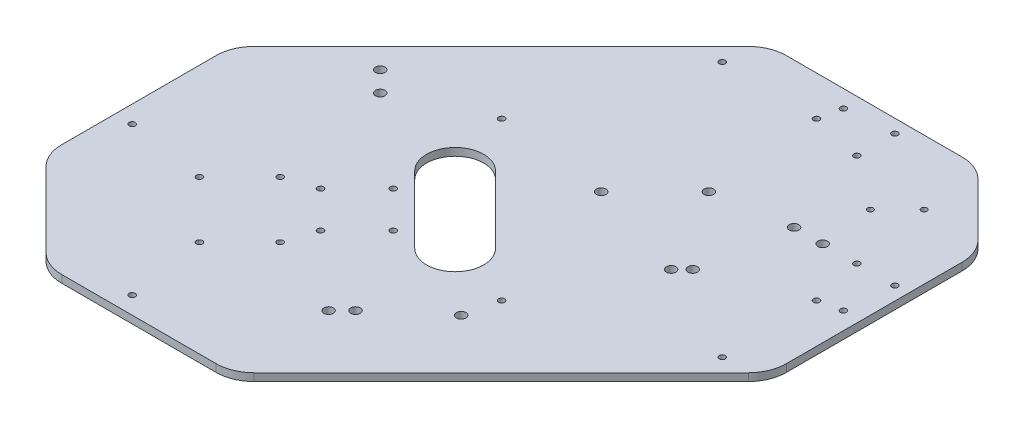
SolidWorks part; units mm, degrees
ref_plane "Front Plane" through (0, 0, 0) normal (0, 0, 1) x (1, 0, 0)
ref_plane "Top Plane" through (0, 0, 0) normal (0, 1, 0) x (1, 0, 0)
ref_plane "Right Plane" through (0, 0, 0) normal (1, 0, 0) x (0, 0, -1)
sketch "Sketch2" plane through (0, 0, 0) normal (0, 1, 0) x (1, 0, 0)
  line L0 (-139.1421, 9.3503) -> (-9.3503, 139.1421)
  line L1 (-150, 150) -> (150, 150) construction
  line L2 (-150, 150) -> (-150, -150) construction
  line L3 (-150, -150) -> (150, -150) construction
  line L4 (150, 150) -> (150, -150) construction
  line L5 (111.3604, 139.1421) -> (139.1421, 111.3604)
  line L6 (-139.1421, -100.0467) -> (-100.0467, -139.1421)
  line L7 (139.1421, -9.3503) -> (9.3503, -139.1421)
  line L8 (150, 150) -> (-150, -150) construction
  line L9 (-29.7918, 5.5635) -> (5.5635, -29.7918) construction
  line L10 (-19.1852, 16.1701) -> (16.1701, -19.1852)
  line L11 (-145, -4.7918) -> (-145, -85.9045)
  line L12 (-85.9045, -145) -> (-4.7918, -145)
  line L13 (145, 4.7918) -> (145, 97.2183)
  line L14 (4.7918, 145) -> (97.2183, 145)
  line L15 (-135.8579, -58.0761) -> (-58.0761, -135.8579) construction
  line L16 (41.4591, 124.1906) -> (124.1906, 41.4591) construction
  line L17 (41.4591, 124.1906) -> (-41.2724, 41.4591) construction
  line L18 (-41.2724, 41.4591) -> (41.4591, -41.2724) construction
  line L19 (124.1906, 41.4591) -> (41.4591, -41.2724) construction
  line L20 (-40.3984, -5.0431) -> (-5.0431, -40.3984)
  line L21 (-72.9254, -43.2269) -> (-43.2269, -72.9254) construction
  line L22 (-72.9254, -43.2269) -> (-94.1386, -64.4401) construction
  line L23 (-94.1386, -64.4401) -> (-64.4401, -94.1386) construction
  line L24 (-37.9236, -18.8317) -> (-18.8317, -37.9236) construction
  line L25 (-37.9236, -18.8317) -> (-57.0155, -37.9236) construction
  line L26 (-57.0155, -37.9236) -> (-37.9236, -57.0155) construction
  line L27 (-18.8317, -37.9236) -> (-37.9236, -57.0155) construction
  line L28 (-43.2269, -72.9254) -> (-64.4401, -94.1386) construction
  line L29 (138, 68.8629) -> (118, 68.8629) construction
  line L30 (68.8629, 138) -> (68.8629, 118) construction
  line L31 (68.8629, 118) -> (118, 68.8629) construction
  line L32 (77.5216, 23.0743) -> (71.8647, 17.4175) construction
  line L33 (46.4089, 62.6723) -> (18.1246, 34.388) construction
  line L34 (-9.099, 125.2513) -> (125.2513, -9.099) construction
  line L35 (77.5216, 23.0743) -> (42.1662, 58.4297) construction
  line L36 (43.934, 135.8579) -> (135.8579, 43.934) construction
  line L37 (-95.4358, 31.8434) -> (-84.8292, 21.2368) construction
  line L38 (85, 68.8629) -> (100, 68.8629) construction
  line L39 (7.6848, -84.2391) -> (0.6137, -91.3101) construction
  arc A0 (-19.1852, 16.1701) -> (-40.3984, -5.0431) centre (-29.7918, 5.5635) ccw
  arc A1 (-5.0431, -40.3984) -> (16.1701, -19.1852) centre (5.5635, -29.7918) ccw
  circle A2 centre (-94.1386, -64.4401) radius 1.6
  circle A3 centre (-64.4401, -94.1386) radius 1.6
  arc A4 (-145, -4.7918) -> (-139.1421, 9.3503) centre (-125, -4.7918) cw
  arc A5 (-145, -85.9045) -> (-139.1421, -100.0467) centre (-125, -85.9045) ccw
  arc A6 (-85.9045, -145) -> (-100.0467, -139.1421) centre (-85.9045, -125) cw
  arc A7 (-4.7918, -145) -> (9.3503, -139.1421) centre (-4.7918, -125) ccw
  arc A8 (145, 4.7918) -> (139.1421, -9.3503) centre (125, 4.7918) cw
  arc A9 (145, 97.2183) -> (139.1421, 111.3604) centre (125, 97.2183) ccw
  arc A10 (97.2183, 145) -> (111.3604, 139.1421) centre (97.2183, 125) cw
  arc A11 (4.7918, 145) -> (-9.3503, 139.1421) centre (4.7918, 125) ccw
  circle A12 centre (-41.2724, 41.4591) radius 1.6
  circle A13 centre (41.4591, -41.2724) radius 1.6
  circle A14 centre (124.1906, 41.4591) radius 1.6
  circle A15 centre (41.4591, 124.1906) radius 1.6
  circle A16 centre (-135.8579, -58.0761) radius 1.6
  circle A17 centre (-58.0761, -135.8579) radius 1.6
  circle A18 centre (-43.2269, -72.9254) radius 1.6
  circle A19 centre (-72.9254, -43.2269) radius 1.6
  circle A20 centre (111.1091, 111.1091) radius 1.5
  circle A21 centre (96.967, 96.967) radius 1.5
  circle A22 centre (-57.0155, -37.9236) radius 1.6
  circle A23 centre (-37.9236, -57.0155) radius 1.6
  circle A24 centre (-18.8317, -37.9236) radius 1.6
  circle A25 centre (-37.9236, -18.8317) radius 1.6
  circle A26 centre (138, 68.8629) radius 1.6
  circle A27 centre (118, 68.8629) radius 1.6
  circle A28 centre (68.8629, 138) radius 1.6
  circle A29 centre (68.8629, 118) radius 1.6
  circle A30 centre (-9.099, 125.2513) radius 1.6
  circle A31 centre (125.2513, -9.099) radius 1.6
  circle A32 centre (77.5216, 23.0743) radius 2.5
  circle A33 centre (71.8647, 17.4175) radius 2.5
  circle A34 centre (43.934, 135.8579) radius 1.6
  circle A35 centre (135.8579, 43.934) radius 1.6
  circle A36 centre (18.1246, 34.388) radius 2.5
  circle A37 centre (46.4089, 62.6723) radius 2.5
  circle A38 centre (-95.4358, 31.8434) radius 2.5
  circle A39 centre (-84.8292, 21.2368) radius 2.5
  circle A40 centre (85, 68.8629) radius 2.5
  circle A41 centre (100, 68.8629) radius 2.5
  circle A42 centre (37.57, -58.5965) radius 2.5
  circle A43 centre (7.6848, -84.2391) radius 2.5
  circle A44 centre (0.6137, -91.3101) radius 2.5
  point P6 (82.8249, 82.8249)
  point P8 (89.8959, 89.8959)
  point P10 (58.0761, 58.0761)
  point P11 (-28.3776, -28.3776)
  point P13 (-12.1142, -12.1142)
  point P52 (-58.0761, -58.0761)
  point P53 (-96.967, -96.967)
  point P82 (93.4315, 93.4315)
  point P90 (74.6931, 20.2459)
  dimension "D7" = 3.2
  dimension "D8" = 3.2
  dimension "D9" = 3.2
  dimension "D10" = 3.2
  dimension "D16" = 20
  dimension "D17" = 20
  dimension "D18" = 20
  dimension "D19" = 20
  dimension "D20" = 20
  dimension "D21" = 20
  dimension "D24" = 20
  dimension "D25" = 20
  dimension "D38" = 20
  dimension "D39" = 3
  dimension "D41" = 20
  dimension "D42" = 3.2
  dimension "D46" = 5
  dimension "D53" = 15
  dimension "D54" = 5
  dimension "D57" = 5
  dimension "D58" = 5
  dimension "D60" = 5
  dimension "D63" = 5
  dimension "D64" = 10
  dimension "D1" = 190
  dimension "D2" = 300
  dimension "D3" = 300
  dimension "D4" = 110
  dimension "D5" = 95
  dimension "D6" = 145
  dimension "D11" = 85
  dimension "D12" = 130
  dimension "D13" = 75
  dimension "D14" = 35
  dimension "D15" = 43
  dimension "D22" = 5
  dimension "D23" = 5
  dimension "D26" = 5
  dimension "D27" = 5
  dimension "D28" = 117
  dimension "D29" = 117
  dimension "D30" = 27
  dimension "D31" = 27
  dimension "D32" = 195
  dimension "D33" = 30
  dimension "D34" = 50
  dimension "D35" = 42
  dimension "D36" = 30
  dimension "D37" = 100
  dimension "D40" = 20
  dimension "D43" = 27
  dimension "D44" = 20
  dimension "D45" = 80
  dimension "D47" = 20
  dimension "D48" = 8
  dimension "D49" = 50
  dimension "D50" = 6
  dimension "D51" = 40
  dimension "D52" = 50
  dimension "D55" = 15
  dimension "D56" = 15
  dimension "D59" = 45
  dimension "D61" = 37
  dimension "D62" = 192
  dimension "D65" = 40
  dimension "D66" = 3
extrude "Boss-Extrude1" add sketch "Sketch2" along normal blind 4
